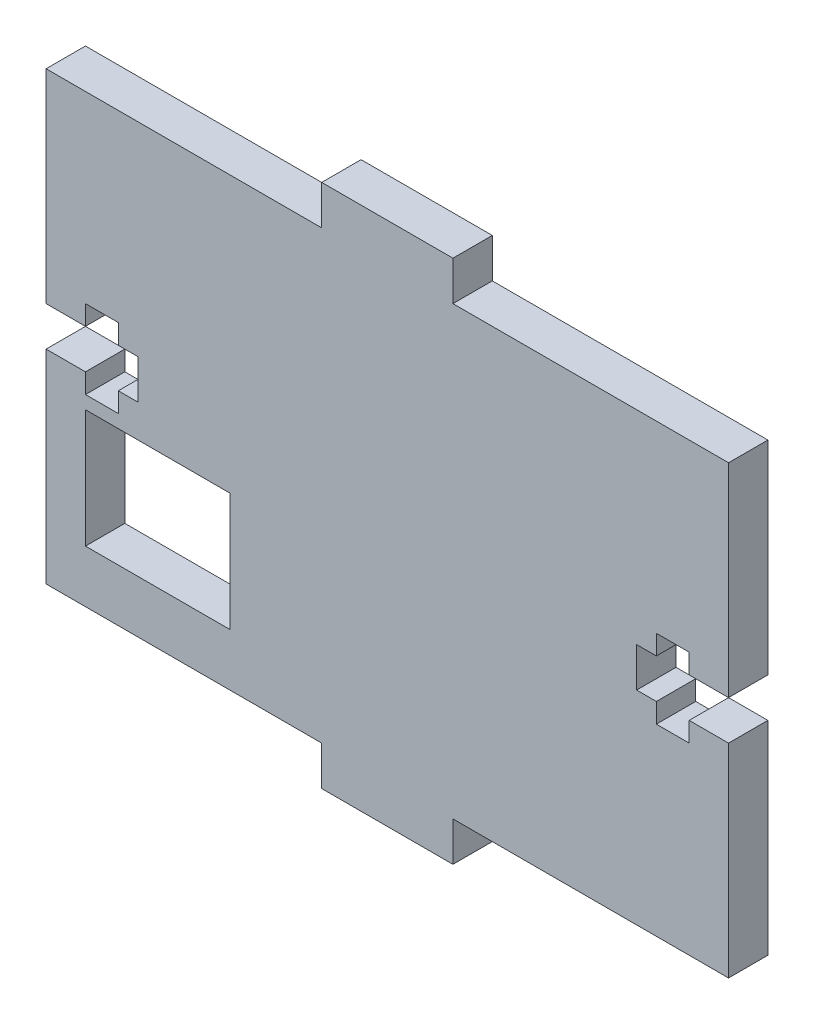
SolidWorks part; units mm, degrees
ref_plane "Front Plane" through (0, 0, 0) normal (0, 0, 1) x (1, 0, 0)
ref_plane "Top Plane" through (0, 0, 0) normal (0, 1, 0) x (1, 0, 0)
ref_plane "Right Plane" through (0, 0, 0) normal (1, 0, 0) x (0, 0, -1)
sketch "Sketch1" plane through (0, 0, 0) normal (0, 0, 1) x (1, 0, 0)
  line L0 (0, 0) -> (0, -24.1244) construction
  line L1 (-26, -17) -> (-5, -17)
  line L2 (-26, -17) -> (-26, -1.5)
  line L3 (-26, 17) -> (-5, 17)
  line L4 (26, -17) -> (26, -1.5)
  line L5 (-26, -17) -> (26, 17) construction
  line L6 (-26, 17) -> (26, -17) construction
  line L7 (19, -1.5) -> (19, 1.5) construction
  line L8 (5, 17) -> (26, 17)
  line L9 (20.5, 3) -> (23, 3) construction
  line L10 (19, 1.5) -> (20.5, 1.5) construction
  line L11 (20.5, 1.5) -> (20.5, 3) construction
  line L12 (20.5, -1.5) -> (19, -1.5) construction
  line L13 (20.5, -3) -> (20.5, -1.5) construction
  line L14 (23, -3) -> (20.5, -3) construction
  line L15 (23, -1.5) -> (23, -3) construction
  line L16 (26, -1.5) -> (23, -1.5) construction
  line L17 (23, 1.5) -> (26, 1.5) construction
  line L18 (23, 3) -> (23, 1.5) construction
  line L19 (-26, 1.5) -> (-23, 1.5) construction
  line L20 (5, -17) -> (26, -17)
  line L21 (5, 17) -> (5, 20)
  line L22 (5, 20) -> (-5, 20)
  line L23 (-5, 17) -> (-5, 20)
  line L24 (5, 17) -> (-5, 20) construction
  line L25 (5, 20) -> (-5, 17) construction
  line L26 (-23, -1.5) -> (-26, -1.5) construction
  line L27 (5, -17) -> (5, -20)
  line L28 (5, -20) -> (-5, -20)
  line L29 (-5, -17) -> (-5, -20)
  line L30 (5, -17) -> (-5, -20) construction
  line L31 (5, -20) -> (-5, -17) construction
  line L32 (-23, -4) -> (-12, -4)
  line L33 (-23, -4) -> (-23, -13)
  line L34 (-23, -13) -> (-12, -13)
  line L35 (-12, -4) -> (-12, -13)
  line L36 (-23, -4) -> (-12, -13) construction
  line L37 (-23, -13) -> (-12, -4) construction
  line L38 (-23, -3) -> (-23, -1.5) construction
  line L39 (-20.5, -3) -> (-23, -3) construction
  line L40 (-20.5, -1.5) -> (-20.5, -3) construction
  line L41 (-19, -1.5) -> (-20.5, -1.5) construction
  line L42 (-20.5, 1.5) -> (-19, 1.5) construction
  line L43 (-19, 1.5) -> (-19, -1.5) construction
  line L44 (-20.5, 3) -> (-20.5, 1.5) construction
  line L45 (-23, 3) -> (-20.5, 3) construction
  line L46 (19, -1.5) -> (19, 1.5)
  line L47 (20.5, 3) -> (23, 3)
  line L48 (19, 1.5) -> (20.5, 1.5)
  line L49 (20.5, 1.5) -> (20.5, 3)
  line L50 (20.5, -1.5) -> (19, -1.5)
  line L51 (20.5, -3) -> (20.5, -1.5)
  line L52 (23, -3) -> (20.5, -3)
  line L53 (23, -1.5) -> (23, -3)
  line L54 (26, -1.5) -> (23, -1.5)
  line L55 (23, 1.5) -> (26, 1.5)
  line L56 (23, 3) -> (23, 1.5)
  line L57 (-26, 1.5) -> (-23, 1.5)
  line L58 (-23, -1.5) -> (-26, -1.5)
  line L59 (-23, -3) -> (-23, -1.5)
  line L60 (-20.5, -3) -> (-23, -3)
  line L61 (-20.5, -1.5) -> (-20.5, -3)
  line L62 (-19, -1.5) -> (-20.5, -1.5)
  line L63 (-20.5, 1.5) -> (-19, 1.5)
  line L64 (-19, 1.5) -> (-19, -1.5)
  line L65 (-20.5, 3) -> (-20.5, 1.5)
  line L66 (-23, 3) -> (-20.5, 3)
  line L67 (-23, 3) -> (-23, 1.5)
  line L68 (-26, 1.5) -> (-26, 17)
  line L69 (26, 1.5) -> (26, 17)
  point P0 (0, 0)
  point P5 (0, 0)
  point P6 (0, 0)
  point P22 (0, 18.5)
  point P27 (0, -18.5)
  point P32 (-17.5, -8.5)
  dimension "D1" = 34
  dimension "D2" = 52
  dimension "D3" = 15.5
  dimension "D4" = 21
  dimension "D5" = 3
  dimension "D6" = 10
  dimension "D7" = 3
  dimension "D8" = 10
  dimension "D9" = 1.5
extrude "Boss-Extrude1" add sketch "Sketch1" along normal blind 3
